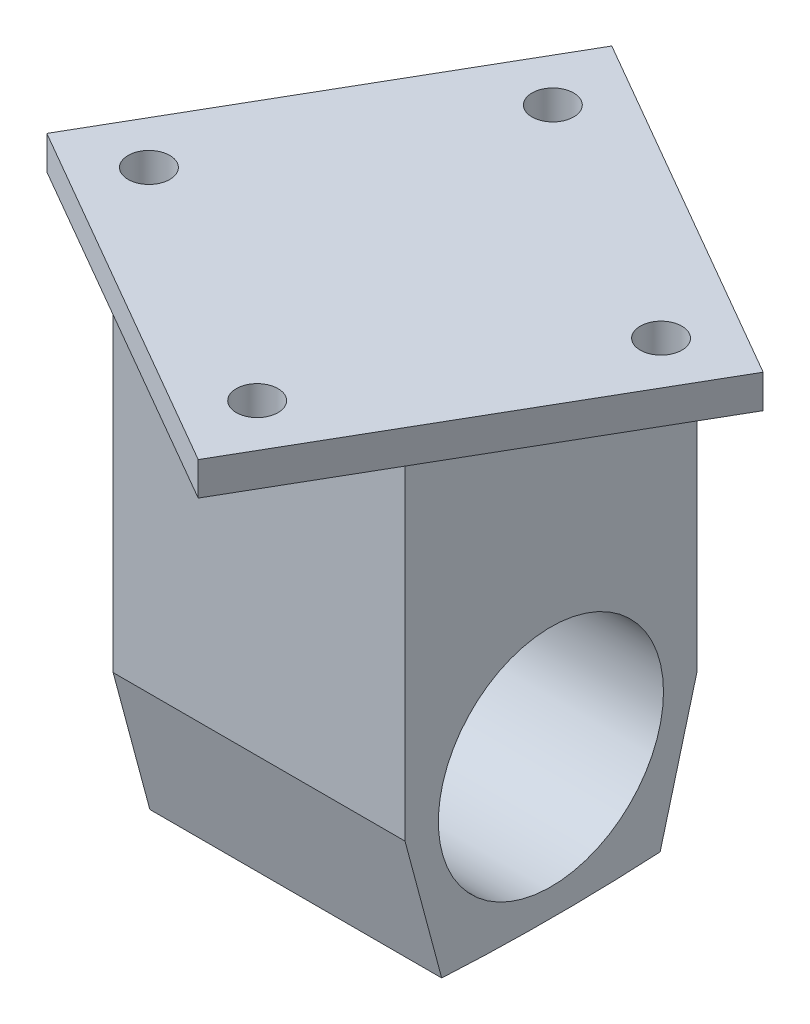
SolidWorks part; units mm, degrees
material "ABS"
ref_plane "Front Plane" through (0, 0, 0) normal (0, 0, 1) x (1, 0, 0)
ref_plane "Top Plane" through (0, 0, 0) normal (0, 1, 0) x (1, 0, 0)
ref_plane "Right Plane" through (0, 0, 0) normal (1, 0, 0) x (0, 0, -1)
sketch "Sketch1" plane through (0, 0, 0) normal (0, 1, 0) x (1, 0, 0)
  line L1 (-22.225, -22.225) -> (22.225, -22.225)
  line L2 (-22.225, -22.225) -> (-22.225, 22.225)
  line L3 (-22.225, 22.225) -> (22.225, 22.225)
  line L4 (22.225, -22.225) -> (22.225, 22.225)
  line L5 (-22.225, -22.225) -> (22.225, 22.225) construction
  line L6 (-22.225, 22.225) -> (22.225, -22.225) construction
  point P0 (0, 0)
extrude "Boss-Extrude1" add sketch "Sketch1" along normal blind 50.292
sketch "Sketch2" plane through (22.225, 0, 0) normal (1, 0, 0) x (0, 0, -1)
  line L0 (-22.225, 0) -> (-16.6371, -20.8543)
  line L1 (22.225, 0) -> (16.6371, -20.8543)
  line L2 (-22.225, 0) -> (22.225, 0)
  line L3 (-22.225, 0) -> (22.225, 0) construction
  arc A1 (16.6371, -20.8543) -> (-16.6371, -20.8543) centre (0, 278.6719) cw
  dimension "D1" = 21.59
  dimension "D2" = 21.59
  dimension "D3" = 75
  dimension "D4" = 75
extrude "Boss-Extrude2" add sketch "Sketch2" against normal up to vertex (44.45 mm away) contours L0 A1 L1 L2 up to point (-22.225, 0, -22.225)
sketch "Sketch3" plane through (22.225, 0, 0) normal (1, 0, 0) x (0, 0, -1)
  circle A0 centre (0, 0) radius 17.145
extrude "Cut-Extrude1" cut sketch "Sketch3" against normal blind 127 contours A0
sketch "Sketch4" plane through (0, 50.292, 0) normal (0, 1, 0) x (1, 0, 0)
  line L0 (-46.8473, -12.5527) -> (46.8473, 12.5527) construction
  line L5 (13.6389, -50.901) -> (-13.6389, 50.901) construction
  line L6 (43.0243, 11.5283) -> (11.5283, -43.0243)
  line L11 (11.5283, -43.0243) -> (-43.0243, -11.5283)
  line L12 (-43.0243, -11.5283) -> (-11.5283, 43.0243)
  line L13 (-11.5283, 43.0243) -> (43.0243, 11.5283)
  line L14 (11.5283, -43.0243) -> (-11.5283, 43.0243) construction
  line L15 (-43.0243, -11.5283) -> (43.0243, 11.5283) construction
  point P1 (0, 0)
  point P4 (0, 0)
  point P11 (0, 0)
  dimension "D1" = 62.992
  dimension "D2" = 62.992
  dimension "D3" = 0
  dimension "D4" = 0
extrude "Boss-Extrude3" add sketch "Sketch4" along normal blind 5.08
sketch "Sketch5" plane through (0, 55.372, 0) normal (0, 1, 0) x (1, 0, 0)
  line L2 (30.7571, 8.2413) -> (43.0243, 11.5283) construction
  line L3 (8.2413, -30.7571) -> (11.5283, -43.0243) construction
  line L4 (-30.7571, -8.2413) -> (-43.0243, -11.5283) construction
  line L5 (-8.2413, 30.7571) -> (-11.5283, 43.0243) construction
  line L6 (-11.5283, 43.0243) -> (-43.0243, -11.5283) construction
  line L7 (43.0243, 11.5283) -> (-11.5283, 43.0243) construction
  line L8 (-43.0243, -11.5283) -> (11.5283, -43.0243) construction
  circle A0 centre (30.7571, 8.2413) radius 3.175
  circle A1 centre (8.2413, -30.7571) radius 3.175
  circle A2 centre (-8.2413, 30.7571) radius 3.175
  circle A3 centre (-30.7571, -8.2413) radius 3.175
  dimension "D2" = 6.35
  dimension "D4" = 6.35
  dimension "D11" = 6.35
  dimension "D12" = 6.35
  dimension "D1" = 12.7
  dimension "D3" = 45
  dimension "D5" = 12.7
  dimension "D6" = 45
  dimension "D7" = 12.7
  dimension "D8" = 45
  dimension "D9" = 12.7
  dimension "D10" = 45
extrude "Cut-Extrude2" cut sketch "Sketch5" against normal through all
